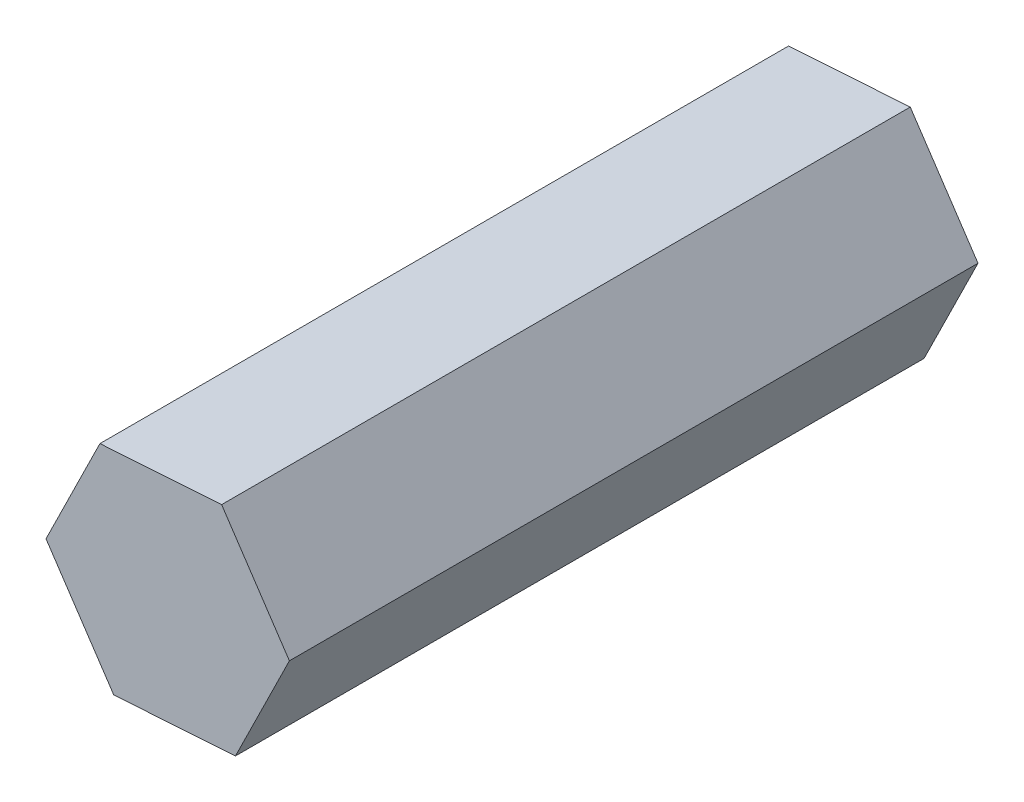
SolidWorks part; units mm, degrees
ref_plane "Front Plane" through (0, 0, 0) normal (0, 0, 1) x (1, 0, 0)
ref_plane "Top Plane" through (0, 0, 0) normal (0, 1, 0) x (1, 0, 0)
ref_plane "Right Plane" through (0, 0, 0) normal (1, 0, 0) x (0, 0, -1)
sketch "Sketch1" plane through (0, 0, 0) normal (0, 0, 1) x (1, 0, 0)
  line L1 (3.2424, 6.5765) -> (-4.0742, 6.0962)
  line L2 (-4.0742, 6.0962) -> (-7.3166, -0.4803)
  line L3 (-7.3166, -0.4803) -> (-3.2424, -6.5765)
  line L4 (-3.2424, -6.5765) -> (4.0742, -6.0962)
  line L5 (4.0742, -6.0962) -> (7.3166, 0.4803)
  line L6 (7.3166, 0.4803) -> (3.2424, 6.5765)
  circle A0 centre (0, 0) radius 6.35 construction
  dimension "D1" = 12.7
extrude "Boss-Extrude1" add sketch "Sketch1" along normal blind 41.402
